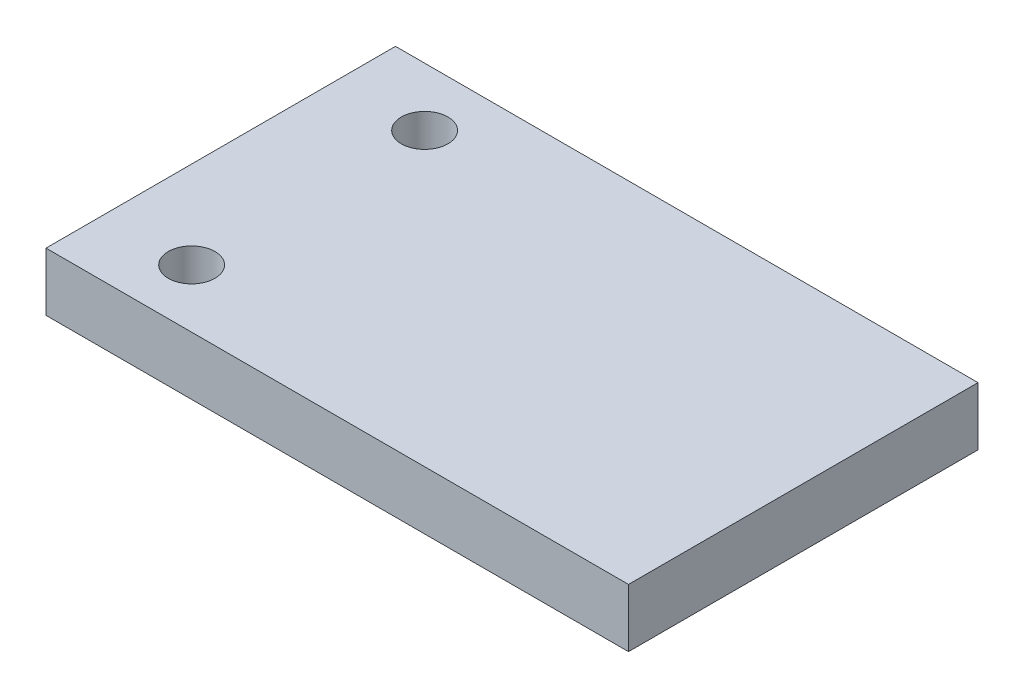
SolidWorks part; units mm, degrees
ref_plane "Front Plane" through (0, 0, 0) normal (0, 0, 1) x (1, 0, 0)
ref_plane "Top Plane" through (0, 0, 0) normal (0, 1, 0) x (1, 0, 0)
ref_plane "Right Plane" through (0, 0, 0) normal (1, 0, 0) x (0, 0, -1)
sketch "Sketch1" plane through (0, 0, 0) normal (0, 1, 0) x (1, 0, 0)
  line L1 (25, -15) -> (-25, -15)
  line L2 (25, -15) -> (25, 15)
  line L3 (25, 15) -> (-25, 15)
  line L4 (-25, -15) -> (-25, 15)
  line L5 (25, -15) -> (-25, 15) construction
  line L6 (25, 15) -> (-25, -15) construction
  point P0 (0, 0)
  dimension "D1" = 30
  dimension "D2" = 50
extrude "Boss-Extrude1" add sketch "Sketch1" along normal blind 5
sketch "Sketch2" plane through (0, 5, 0) normal (0, 1, 0) x (1, 0, 0)
  line L0 (-25, 15) -> (-25, -15) construction
  circle A0 centre (-17.5, 10) radius 2
  circle A1 centre (-17.5, -10) radius 2
  dimension "D1" = 20
  dimension "D2" = 10
  dimension "D3" = 7.5
extrude "Cut-Extrude1" cut sketch "Sketch2" against normal blind 5
